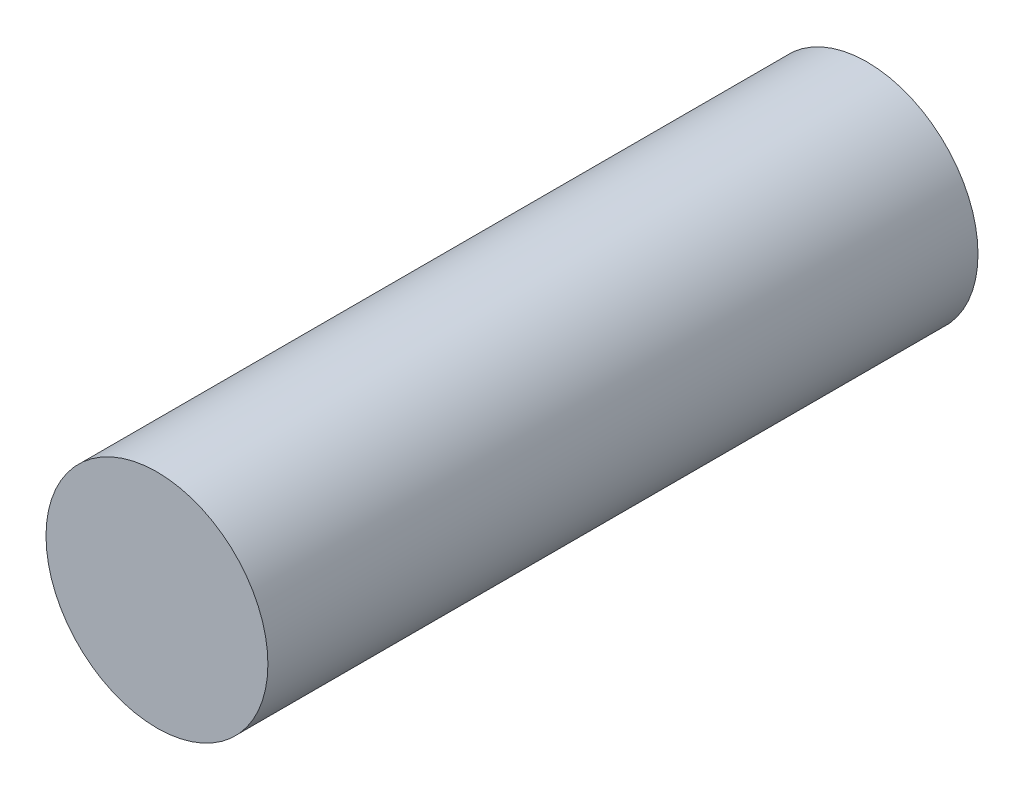
SolidWorks part; units mm, degrees
ref_plane "Front Plane" through (0, 0, 0) normal (0, 0, 1) x (1, 0, 0)
ref_plane "Top Plane" through (0, 0, 0) normal (0, 1, 0) x (1, 0, 0)
ref_plane "Right Plane" through (0, 0, 0) normal (1, 0, 0) x (0, 0, -1)
sketch "Sketch1" plane through (0, 0, 0) normal (0, 0, 1) x (1, 0, 0)
  circle A0 centre (0, 0) radius 3.9688
  dimension "D1" = 7.9375
extrude "Boss-Extrude1" add sketch "Sketch1" along normal blind 25.4
